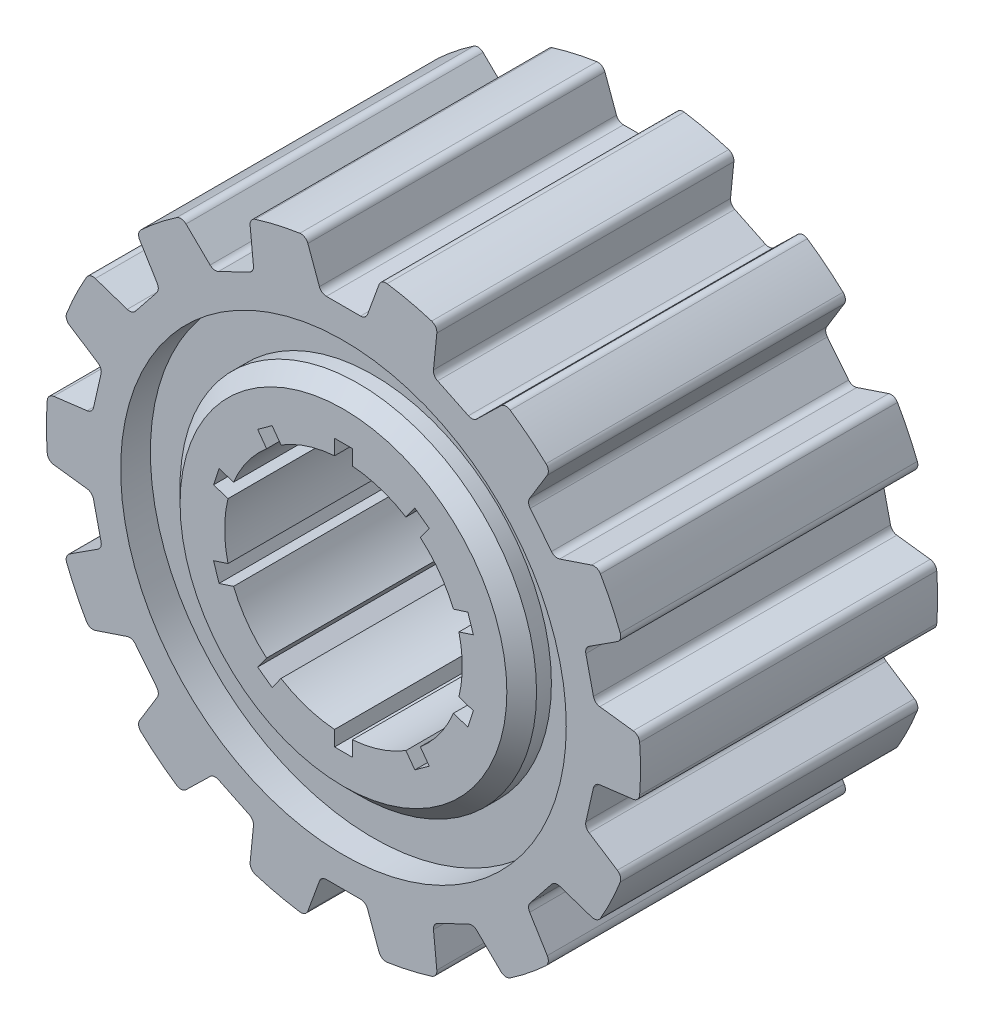
SolidWorks part; units mm, degrees
ref_plane "Front Plane" through (0, 0, 0) normal (0, 0, 1) x (1, 0, 0)
ref_plane "Top Plane" through (0, 0, 0) normal (0, 1, 0) x (1, 0, 0)
ref_plane "Right Plane" through (0, 0, 0) normal (1, 0, 0) x (0, 0, -1)
sketch "Sketch1" plane through (0, 0, 0) normal (0, 0, 1) x (1, 0, 0)
  line L0 (0, 0) -> (0, 5.7262) construction
  line L1 (2.4023, 3.8169) -> (2.8877, 3.4642)
  line L2 (-0.3, 4.5) -> (0.3, 4.5)
  line L3 (-0.3, 4.5) -> (-0.3, 3.9887)
  line L5 (0.3, 4.5) -> (0.3, 3.9887)
  line L6 (-0.3, 4.5) -> (0.3, 2.6918) construction
  line L7 (-0.3, 2.6918) -> (0.3, 4.5) construction
  line L8 (2.8877, 3.4642) -> (2.5872, 3.0506)
  line L9 (2.4023, 3.8169) -> (2.1018, 3.4033)
  line L10 (4.187, 1.6759) -> (4.3725, 1.1053)
  line L11 (4.3725, 1.1053) -> (3.8862, 0.9473)
  line L12 (4.187, 1.6759) -> (3.7008, 1.5179)
  line L13 (4.3725, -1.1053) -> (4.187, -1.6759)
  line L14 (4.187, -1.6759) -> (3.7008, -1.5179)
  line L15 (4.3725, -1.1053) -> (3.8862, -0.9473)
  line L16 (2.8877, -3.4642) -> (2.4023, -3.8169)
  line L17 (2.4023, -3.8169) -> (2.1018, -3.4033)
  line L18 (2.8877, -3.4642) -> (2.5872, -3.0506)
  line L19 (0.3, -4.5) -> (-0.3, -4.5)
  line L20 (-0.3, -4.5) -> (-0.3, -3.9887)
  line L21 (0.3, -4.5) -> (0.3, -3.9887)
  line L22 (-2.4023, -3.8169) -> (-2.8877, -3.4642)
  line L23 (-2.8877, -3.4642) -> (-2.5872, -3.0506)
  line L24 (-2.4023, -3.8169) -> (-2.1018, -3.4033)
  line L25 (-4.187, -1.6759) -> (-4.3725, -1.1053)
  line L26 (-4.3725, -1.1053) -> (-3.8862, -0.9473)
  line L27 (-4.187, -1.6759) -> (-3.7008, -1.5179)
  line L28 (-4.3725, 1.1053) -> (-4.187, 1.6759)
  line L29 (-4.187, 1.6759) -> (-3.7008, 1.5179)
  line L30 (-4.3725, 1.1053) -> (-3.8862, 0.9473)
  line L31 (-2.8877, 3.4642) -> (-2.4023, 3.8169)
  line L32 (-2.4023, 3.8169) -> (-2.1018, 3.4033)
  line L33 (-2.8877, 3.4642) -> (-2.5872, 3.0506)
  circle A1 centre (0, 0) radius 10
  arc A2 (-0.3, 3.9887) -> (-2.1018, 3.4033) centre (0, 0) ccw
  arc A3 (-2.5872, 3.0506) -> (-3.7008, 1.5179) centre (0, 0) ccw
  arc A4 (-3.8862, 0.9473) -> (-3.8862, -0.9473) centre (0, 0) ccw
  arc A5 (-3.7008, -1.5179) -> (-2.5872, -3.0506) centre (0, 0) ccw
  arc A6 (-2.1018, -3.4033) -> (-0.3, -3.9887) centre (0, 0) ccw
  arc A7 (0.3, -3.9887) -> (2.1018, -3.4033) centre (0, 0) ccw
  arc A8 (2.5872, -3.0506) -> (3.7008, -1.5179) centre (0, 0) ccw
  arc A9 (3.8862, -0.9473) -> (3.8862, 0.9473) centre (0, 0) ccw
  arc A10 (3.7008, 1.5179) -> (2.5872, 3.0506) centre (0, 0) ccw
  arc A11 (2.1018, 3.4033) -> (0.3, 3.9887) centre (0, 0) ccw
  point P4 (0, 3.5959)
  point P49 (0, 0)
  dimension "D1" = 20
  dimension "D2" = 4
  dimension "D3" = 0.6
  dimension "D4" = 4.5
  dimension "D5" = 2.6918
  dimension "D6" = 10
extrude "Boss-Extrude1" add sketch "Sketch1" along normal blind 10
sketch "Sketch2" plane through (0, 0, 10) normal (0, 0, 1) x (1, 0, 0)
  line L0 (0, 0) -> (0, 12.1215) construction
  line L1 (-0.75, 8.5) -> (0.75, 8.5)
  line L2 (0.75, 8.5) -> (1.2666, 9.9195)
  line L3 (-0.75, 8.5) -> (-1.2666, 9.9195)
  circle A0 centre (0, 0) radius 10 construction
  circle A1 centre (0, 0) radius 10
  circle M6 centre (0, 0) radius 10
  dimension "D1" = 1.5
  dimension "D2" = 20
  dimension "D3" = 20
  dimension "D4" = 8.5
extrude "Cut-Extrude1" cut sketch "Sketch2" against normal through all contours L1 L0 A1 L3 | L0 L1 L2 M6
pattern_circular "CirPattern1" count 14 over 360 about axis through (0, 0, 0) along (0, 0, 1) of "Cut-Extrude1"
ref_plane "Plane1" through (0, 0, 5) normal (0, 0, 1) x (1, 0, 0)
sketch "Sketch3" plane through (0, 0, 5) normal (0, 0, 1) x (1, 0, 0)
  circle A0 centre (0, 0) radius 6
  circle A1 centre (0, 0) radius 7.5
  dimension "D1" = 15
  dimension "D2" = 12
extrude "Cut-Extrude2" cut sketch "Sketch3" against normal through all from offset 4 offset against normal yes
chamfer "Chamfer1" distance 0.5 angle 45 1 edges at (6, 0, 0)
mirror "Mirror2" about plane through (0, 0, 5) normal (0, 0, 1) of "Cut-Extrude2"
chamfer "Chamfer2" distance 0.5 angle 45 1 edges at (6, 0, 10)
fillet "Fillet1" radius 0.25 56 edges at (-8.5451, 5.1944, 5) (-9.3889, 3.4422, 5) (-8.12, 2.6226, 5) (-8.4538, 1.1602, 5) (-9.9526, 0.9724, 5) (-9.9526, -0.9724, 5) (-8.4538, -1.1602, 5) (-8.12, -2.6226, 5) (-9.3889, -3.4422, 5) (-8.5451, -5.1944, 5) (-7.1132, -4.7133, 5) (-6.178, -5.886, 5) (-6.9656, -7.175, 5) (-5.4451, -8.3875, 5) (-4.3637, -7.3328, 5) (-3.0123, -7.9836, 5) (-3.1627, -9.4867, 5) (-1.2666, -9.9195, 5) (-0.75, -8.5, 5) (0.75, -8.5, 5) (1.2666, -9.9195, 5) (3.1627, -9.4867, 5) (3.0123, -7.9836, 5) (4.3637, -7.3328, 5) (5.4451, -8.3875, 5) (6.9656, -7.175, 5) (6.178, -5.886, 5) (7.1132, -4.7133, 5) (8.5451, -5.1944, 5) (9.3889, -3.4422, 5) (8.12, -2.6226, 5) (8.4538, -1.1602, 5) (9.9526, -0.9724, 5) (8.4538, 1.1602, 5) (8.12, 2.6226, 5) (9.3889, 3.4422, 5) (8.5451, 5.1944, 5) (7.1132, 4.7133, 5) (6.178, 5.886, 5) (6.9656, 7.175, 5) (5.4451, 8.3875, 5) (4.3637, 7.3328, 5) (3.0123, 7.9836, 5) (3.1627, 9.4867, 5) (1.2666, 9.9195, 5) (0.75, 8.5, 5) (-0.75, 8.5, 5) (-1.2666, 9.9195, 5) (-3.1627, 9.4867, 5) (-3.0123, 7.9836, 5) (-4.3637, 7.3328, 5) (-5.4451, 8.3875, 5) (-6.9656, 7.175, 5) (-6.178, 5.886, 5) (-7.1132, 4.7133, 5) (9.9526, 0.9724, 5)
